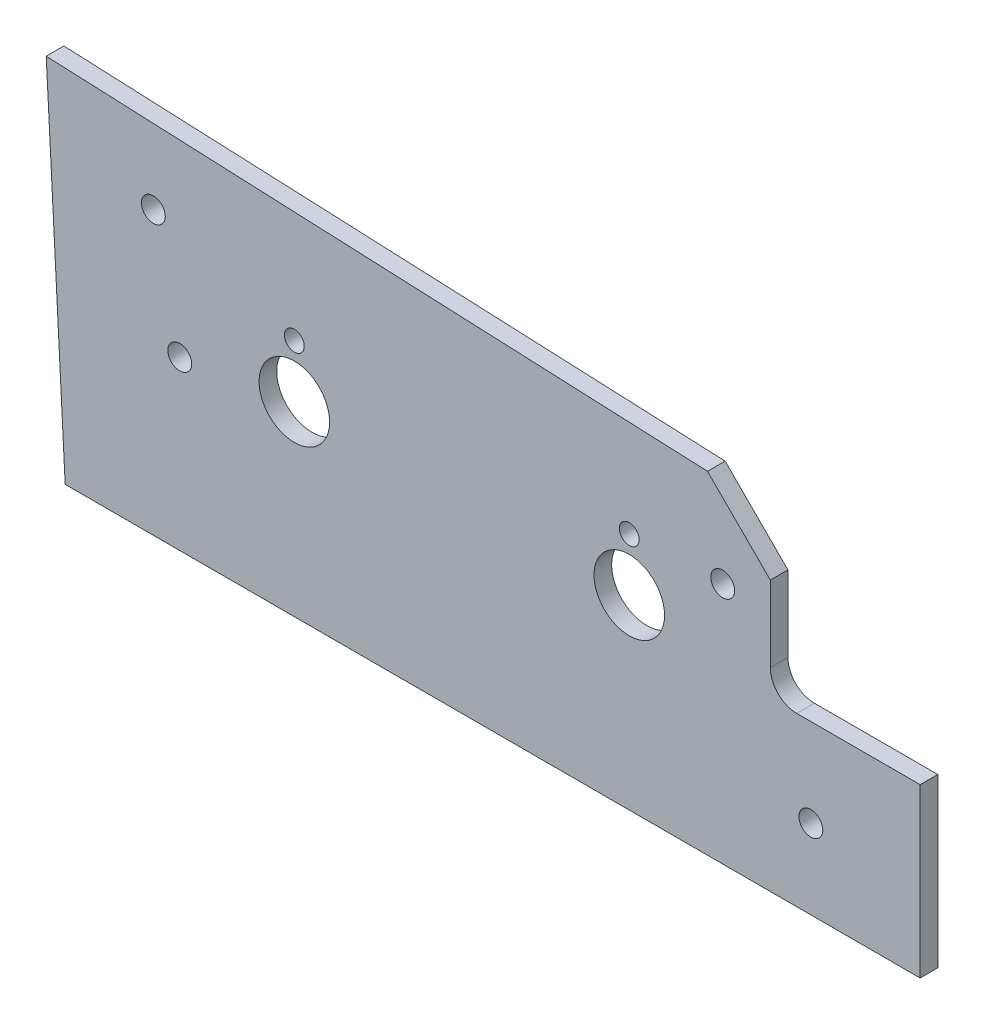
SolidWorks part; units mm, degrees
material "Acrylic (Medium-high impact)"
ref_plane "Front Plane" through (0, 0, 0) normal (0, 0, 1) x (1, 0, 0)
ref_plane "Top Plane" through (0, 0, 0) normal (0, 1, 0) x (1, 0, 0)
ref_plane "Right Plane" through (0, 0, 0) normal (1, 0, 0) x (0, 0, -1)
sketch "Sketch1" plane through (0, 0, 0) normal (0, 0, 1) x (1, 0, 0)
  line L7 (-26.9875, 34.925) -> (-26.9875, 48.5775)
  line L8 (-26.9875, 48.5775) -> (-38.2974, 59.8874)
  line L9 (-38.2974, 59.8874) -> (-157.3986, 65.0875)
  line L10 (-157.3986, 65.0875) -> (-153.9875, 0)
  line L11 (-153.9875, 0) -> (0, 0)
  line L12 (0, 0) -> (0, 30.1625)
  line L13 (0, 30.1625) -> (-22.225, 30.1625)
  line L14 (-26.9875, 34.925) -> (-26.9875, 48.5775)
  line L15 (-26.9875, 48.5775) -> (-38.2974, 59.8874)
  line L16 (-38.2974, 59.8874) -> (-157.3986, 65.0875)
  line L17 (-157.3986, 65.0875) -> (-153.9875, 0)
  line L18 (-153.9875, 0) -> (0, 0)
  line L19 (0, 0) -> (0, 30.1625)
  line L20 (0, 30.1625) -> (-22.225, 30.1625)
  arc A1 (-26.9875, 34.925) -> (-22.225, 30.1625) centre (-22.225, 34.925) ccw
  arc A2 (-26.9875, 34.925) -> (-22.225, 30.1625) centre (-22.225, 34.925) ccw
  dimension "D1" = 0
extrude "Boss-Extrude1" add sketch "Sketch1" against normal blind 3.175
hole_wizard "1/2 (0.5) Diameter Hole1" positions "Sketch3" profile "Sketch2" hole size "1/2" standard "ANSI Inch" end condition through all
sketch "Sketch3" plane through (0, 0, 0) normal (0, 0, 1) x (1, 0, 0)
  point P0 (-112.7125, 33.528)
  point P3 (-52.3875, 33.528)
sketch "Sketch2" plane through (-112.7125, 33.528, 0) normal (1, 0, 0) x (0, -1, 0)
  line L0 (0, 0) -> (0, 3.175)
  line L1 (0, 3.175) -> (6.35, 3.175)
  line L2 (6.35, 3.175) -> (6.35, 0)
  line L5 (6.35, 0) -> (0, 0)
  line L11 (0, -6.35) -> (0, 107.95) construction
  dimension "Thru Hole Dia." = 12.7
  dimension "Thru Hole Depth" = 3.175
hole_wizard "9/64 (0.14063) Diameter Hole1" positions "Sketch5" profile "Sketch4" hole size "9/64" standard "ANSI Inch" end condition through all
sketch "Sketch5" plane through (0, 0, 0) normal (0, 0, 1) x (1, 0, 0)
  point P0 (-112.7125, 43.053)
  point P3 (-52.3875, 43.053)
sketch "Sketch4" plane through (-112.7125, 43.053, 0) normal (1, 0, 0) x (0, -1, 0)
  line L0 (0, 0) -> (0, 3.175)
  line L1 (0, 3.175) -> (1.786, 3.175)
  line L2 (1.786, 3.175) -> (1.786, 0)
  line L5 (1.786, 0) -> (0, 0)
  line L11 (0, -6.35) -> (0, 107.95) construction
  dimension "Thru Hole Dia." = 3.572
  dimension "Thru Hole Depth" = 3.175
hole_wizard "#6 Clearance Hole1" positions "Sketch7" profile "Sketch6" hole size "#6" standard "ANSI Inch" end condition through all
sketch "Sketch7" plane through (0, 0, 0) normal (0, 0, 1) x (1, 0, 0)
  point P0 (-133.35, 30.1625)
  point P3 (-35.56, 43.688)
sketch "Sketch6" plane through (-133.35, 30.1625, 0) normal (1, 0, 0) x (0, -1, 0)
  line L0 (0, 0) -> (0, 3.175)
  line L1 (0, 3.175) -> (2.1526, 3.175)
  line L2 (2.1526, 3.175) -> (2.1526, 0)
  line L5 (2.1526, 0) -> (0, 0)
  line L11 (0, -6.35) -> (0, 107.95) construction
  dimension "Thru Hole Dia." = 4.3053
  dimension "Thru Hole Depth" = 3.175
hole_wizard "#6 Clearance Hole2" positions "Sketch9" profile "Sketch8" hole size "#6" standard "ANSI Inch" end condition through all
sketch "Sketch9" plane through (0, 0, 0) normal (0, 0, 1) x (1, 0, 0)
  point P0 (-138.1125, 50.8)
  point P3 (-19.685, 14.2875)
sketch "Sketch8" plane through (-138.1125, 50.8, 0) normal (1, 0, 0) x (0, -1, 0)
  line L0 (0, 0) -> (0, 3.175)
  line L1 (0, 3.175) -> (2.1526, 3.175)
  line L2 (2.1526, 3.175) -> (2.1526, 0)
  line L5 (2.1526, 0) -> (0, 0)
  line L11 (0, -6.35) -> (0, 107.95) construction
  dimension "Thru Hole Dia." = 4.3053
  dimension "Thru Hole Depth" = 3.175
